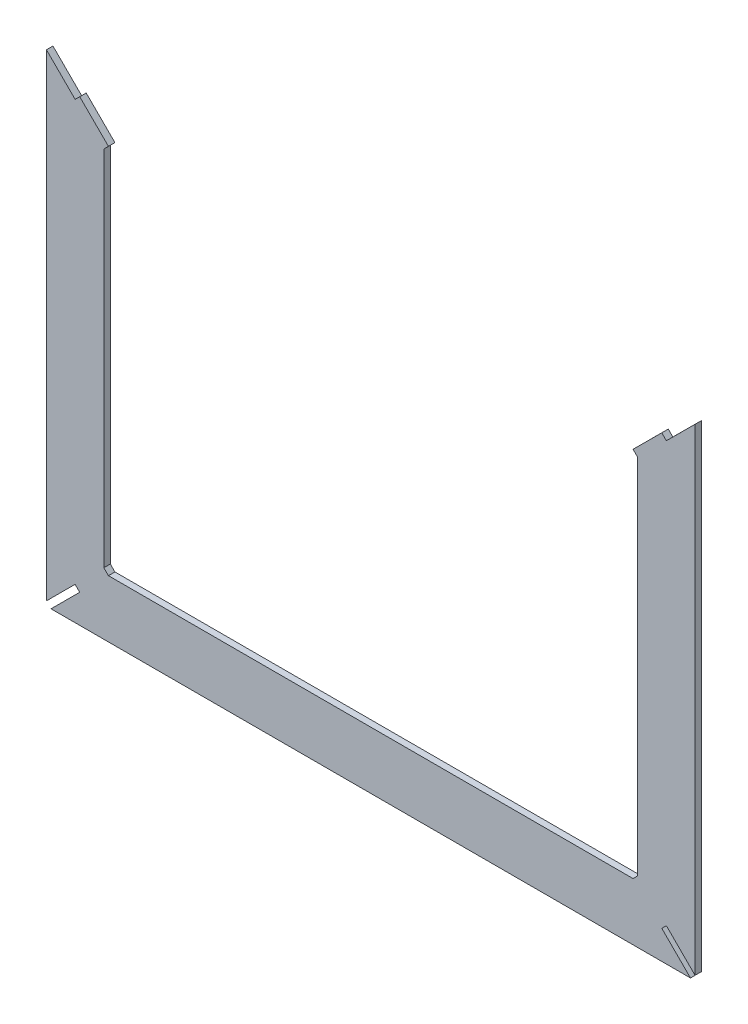
SolidWorks part; units mm, degrees
ref_plane "Plan de face" through (0, 0, 0) normal (0, 0, 1) x (1, 0, 0)
ref_plane "Plan de dessus" through (0, 0, 0) normal (0, 1, 0) x (1, 0, 0)
ref_plane "Plan de droite" through (0, 0, 0) normal (1, 0, 0) x (0, 0, -1)
sketch "Esquisse1" plane through (0, 0, 0) normal (0, 0, 1) x (1, 0, 0)
  line L0 (-72.3879, -137.1329) -> (-69.5594, -134.3045)
  line L1 (-54.6843, 109.8031) -> (-72.3843, 92.1477)
  line L3 (-434.1594, -172.5329) -> (-34.1594, -172.5329) construction
  line L4 (-34.1594, 127.4671) -> (-34.1594, -172.5329) construction
  line L5 (-434.1594, 124.6387) -> (-434.1594, -169.7045)
  line L6 (-431.331, -172.5329) -> (-36.9879, -172.5329)
  line L7 (-34.1594, -169.7045) -> (-34.1594, 124.6264)
  line L8 (-34.1594, 124.6264) -> (-51.8594, 106.9711)
  line L9 (-51.8594, 106.9711) -> (-54.6843, 109.8031)
  line L10 (-395.931, -137.1329) -> (-72.3879, -137.1329)
  line L11 (-34.1594, -169.7045) -> (-51.8371, -152.0268)
  line L12 (-51.8371, -152.0268) -> (-54.6655, -154.8552)
  line L13 (-54.6655, -154.8552) -> (-36.9879, -172.5329)
  line L14 (-431.331, -172.5329) -> (-413.6533, -154.8552)
  line L15 (-413.6533, -154.8552) -> (-416.4818, -152.0268)
  line L16 (-416.4818, -152.0268) -> (-434.1594, -169.7045)
  line L17 (-398.7594, -134.3045) -> (-395.931, -137.1329)
  line L18 (-413.6346, 109.8154) -> (-416.4594, 106.9834)
  line L19 (-416.4594, 106.9834) -> (-434.1594, 124.6387)
  line L20 (-395.9346, 92.16) -> (-398.7594, 89.328)
  line L21 (-69.5594, -134.3045) -> (-69.5594, -137.1329) construction
  line L22 (-69.5594, -137.1329) -> (-72.3879, -137.1329) construction
  line L24 (-395.9346, 92.16) -> (-413.6346, 109.8154)
  line L25 (-398.7594, -134.3045) -> (-398.7594, -137.1329) construction
  line L26 (-398.7594, -137.1329) -> (-395.931, -137.1329) construction
  line L27 (-72.3843, 92.1477) -> (-69.5594, 89.3157)
  line L28 (-69.5594, 89.3157) -> (-69.5594, -134.3045)
  line L29 (-398.7594, 89.328) -> (-398.7594, -134.3045)
  dimension "D1" = 300
  dimension "D2" = 400
  dimension "D3" = 4
  dimension "D4" = 25
  dimension "D5" = 45
  dimension "D6" = 45
  dimension "D7" = 45
  dimension "D8" = 45
  dimension "D9" = 35.4
  dimension "D10" = 4
  dimension "D11" = 35.4
  dimension "D12" = 4
  dimension "D13" = 35.4
  dimension "D14" = 25
extrude "Boss.-Extru.1" add sketch "Esquisse1" along normal blind 4
